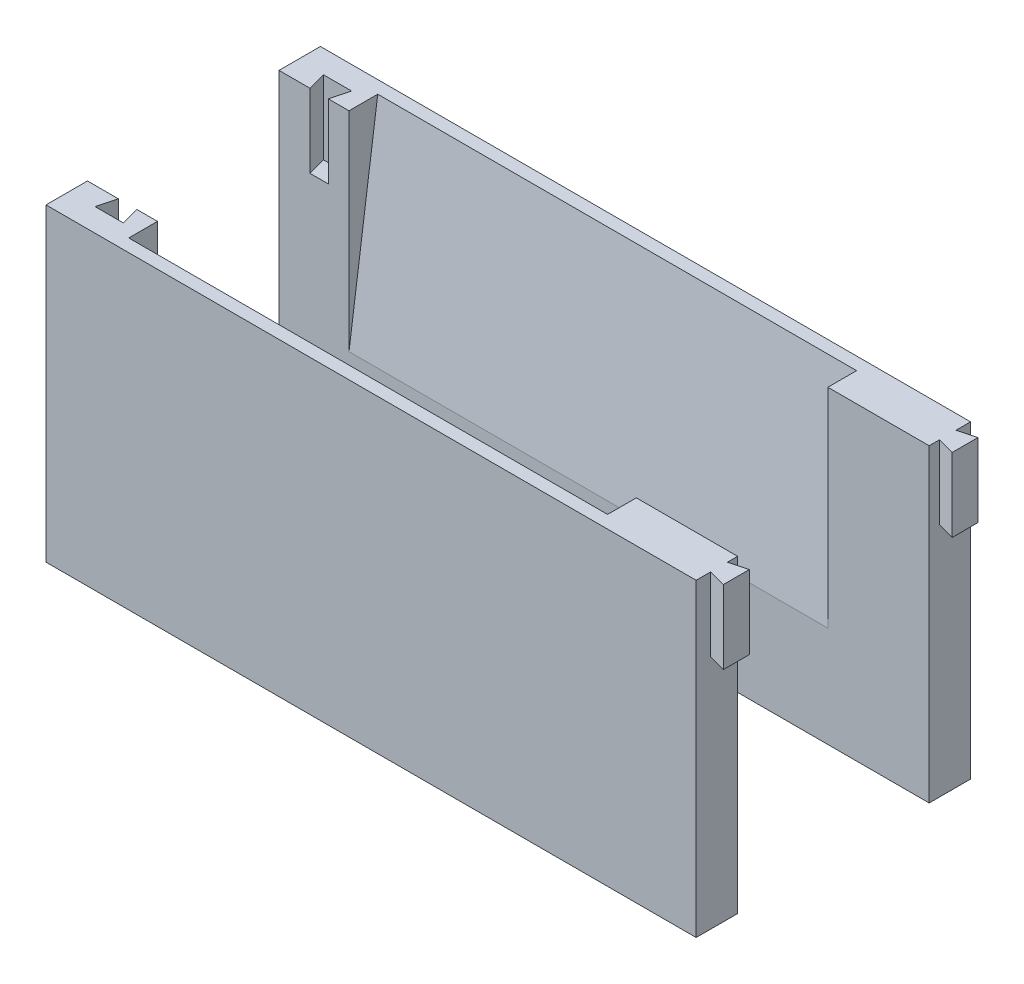
SolidWorks part; units mm, degrees
ref_plane "Front Plane" through (0, 0, 0) normal (0, 0, 1) x (1, 0, 0)
ref_plane "Top Plane" through (0, 0, 0) normal (0, 1, 0) x (1, 0, 0)
ref_plane "Right Plane" through (0, 0, 0) normal (1, 0, 0) x (0, 0, -1)
sketch "Sketch1" plane through (0, 0, 0) normal (0, 0, 1) x (1, 0, 0)
  line L1 (-41.951, 14.0483) -> (46.299, 14.0483)
  line L2 (-41.951, 14.0483) -> (-41.951, -27.9517)
  line L3 (-41.951, -27.9517) -> (46.299, -27.9517)
  line L4 (46.299, 14.0483) -> (46.299, -27.9517)
  dimension "D1" = 88.25
  dimension "D2" = 42
extrude "Boss-Extrude1" add sketch "Sketch1" along normal blind 5
sketch "Sketch2" plane through (0, 14.0483, 0) normal (0, 1, 0) x (1, 0, 0)
  line L0 (-41.951, 0) -> (-37.751, 0) construction
  line L1 (46.299, 0) -> (-41.951, 0) construction
  line L2 (-37.751, 0) -> (-38.4209, -2.5)
  line L3 (-38.4209, -2.5) -> (-34.5812, -2.5)
  line L4 (-34.5812, -2.5) -> (-35.251, 0)
  line L5 (-35.251, 0) -> (-34.6672, 0) construction
  dimension "D1" = 4.2
  dimension "D2" = 105
  dimension "D3" = 105
  dimension "D4" = 2.5
  dimension "D5" = 2.5
  dimension "D6" = 2.5
extrude "Cut-Extrude1" cut sketch "Sketch2" against normal blind 10 and the other way through all
sketch "Sketch3" plane through (0, 14.0483, 0) normal (0, 1, 0) x (1, 0, 0)
  line L0 (46.299, -5) -> (46.299, -3.65) construction
  line L1 (46.299, -5) -> (46.299, 0) construction
  line L2 (46.299, -3.65) -> (48.649, -4.2797)
  line L3 (48.649, -4.2797) -> (48.649, -0.7703)
  line L4 (48.649, -0.7703) -> (46.299, -1.4)
  line L5 (46.299, -1.4) -> (46.299, 0) construction
  line L6 (46.299, -1.4) -> (46.299, -3.65)
  dimension "D1" = 2.25
  dimension "D2" = 1.35
  dimension "D3" = 2.35
  dimension "D4" = 105
  dimension "D5" = 105
extrude "Boss-Extrude2" add sketch "Sketch3" against normal blind 10
ref_plane "Plane1" through (0, 0, -13) normal (0, 0, -1) x (-1, 0, 0)
ref_plane "Plane2" through (-32.451, 0, 0) normal (-1, 0, 0) x (0, 0, 1)
sketch "Sketch6" plane through (-32.451, 0, 0) normal (-1, 0, 0) x (0, 0, 1)
  line L1 (-0.05, 14.0483) -> (-0.05, -27.9517) construction
  line L3 (-0.05, -14.6296) -> (0, 14.0483)
  line L4 (0, 14.0483) -> (3.9, 14.0483)
  line L5 (5, 14.0483) -> (0, 14.0483) construction
  line L6 (-0.05, -14.6296) -> (3.9, 14.0483)
  dimension "D1" = 3.9
extrude "Cut-Extrude2" cut sketch "Sketch6" against normal blind 65
mirror "Mirror3" about plane through (0, 0, -13) normal (0, 0, -1) of bodies 106 102
sketch "Sketch7" plane through (0, 14.0483, 0) normal (0, 1, 0) x (1, 0, 0)
  line L1 (-41.951, -5) -> (46.299, -5)
  line L2 (-41.951, -5) -> (-41.951, -5.63)
  line L3 (-41.951, -5.63) -> (46.299, -5.63)
  line L4 (46.299, -5) -> (46.299, -5.63)
  line L5 (-41.951, 31) -> (46.299, 31)
  line L6 (-41.951, 31) -> (-41.951, 31.6203)
  line L7 (-41.951, 31.6203) -> (46.299, 31.6203)
  line L8 (46.299, 31) -> (46.299, 31.6203)
extrude "Boss-Extrude3" add sketch "Sketch7" against normal blind 42
